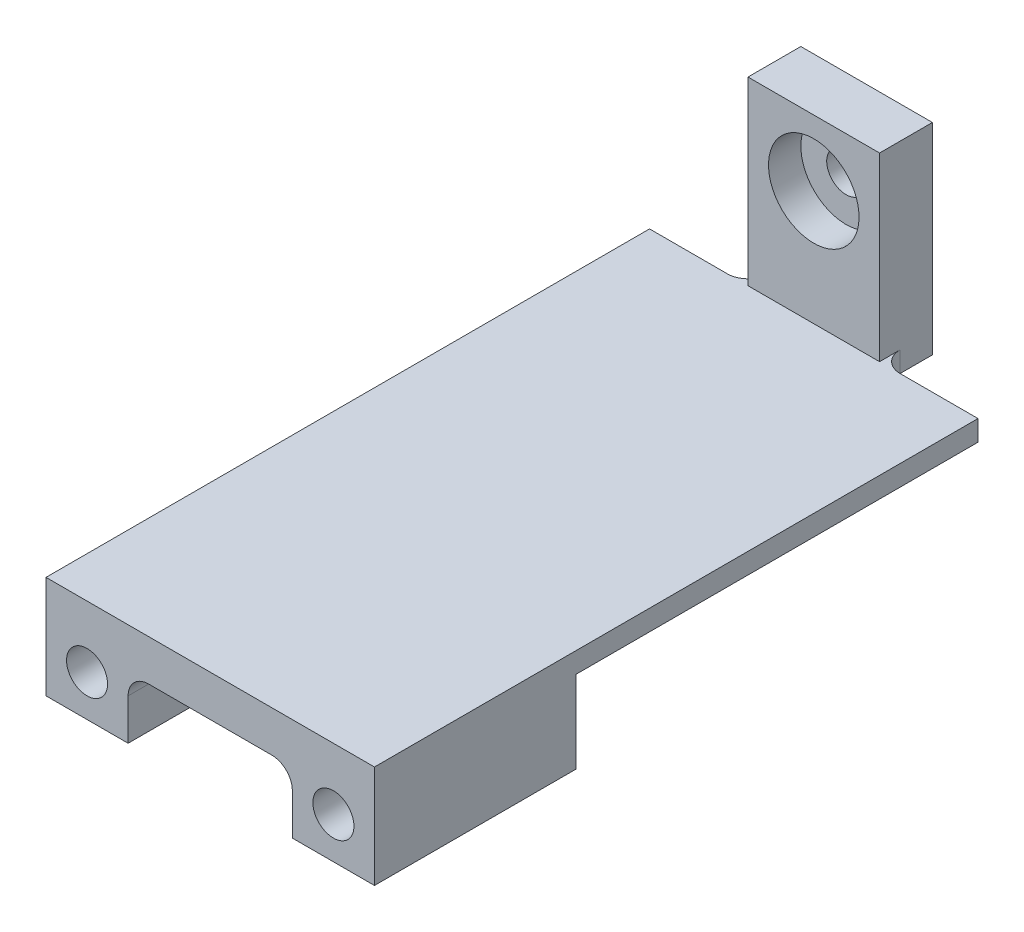
SolidWorks part; units mm, degrees
material "6061-T6 (SS)"
ref_plane "Front Plane" through (0, 0, 0) normal (0, 0, 1) x (1, 0, 0)
ref_plane "Top Plane" through (0, 0, 0) normal (0, 1, 0) x (1, 0, 0)
ref_plane "Right Plane" through (0, 0, 0) normal (1, 0, 0) x (0, 0, -1)
sketch "Sketch1" plane through (0, 0, 0) normal (0, 1, 0) x (1, 0, 0)
  line L1 (-88.9, -50.8) -> (88.9, -50.8)
  line L2 (-88.9, -50.8) -> (-88.9, 50.8)
  line L3 (-88.9, 50.8) -> (88.9, 50.8)
  line L4 (88.9, -50.8) -> (88.9, 50.8)
  line L5 (-88.9, -50.8) -> (88.9, 50.8) construction
  line L6 (-88.9, 50.8) -> (88.9, -50.8) construction
  point P0 (0, 0)
  dimension "D1" = 101.6
  dimension "D2" = 177.8
extrude "Boss-Extrude1" add sketch "Sketch1" along normal blind 12.7
sketch "Sketch2" plane through (0, 0, 50.8) normal (0, 0, 1) x (1, 0, 0)
  line L0 (12.7, -19.05) -> (12.7, 0)
  line L1 (-88.9, 0) -> (88.9, 0) construction
  line L3 (12.7, -19.05) -> (-12.7, -19.05)
  line L4 (-12.7, -19.05) -> (-12.7, 0)
  line L5 (12.7, 0) -> (-12.7, 0)
  point P0 (0, 0)
  point P2 (0, -19.05)
  dimension "D2" = 25.4
  dimension "D3" = 19.05
extrude "Boss-Extrude2" add sketch "Sketch2" against normal up to surface (101.6 mm away) up to face at (0, 6.35, -50.8)
sketch "Sketch3" plane through (0, 0, 50.8) normal (0, 0, 1) x (1, 0, 0)
  line L0 (0, 0) -> (0, -6.35) construction
  circle A1 centre (0, -6.35) radius 6.35
  point P4 (0, -3.175)
  dimension "D2" = 12.7
  dimension "D1" = 6.35
extrude "Cut-Extrude1" cut sketch "Sketch3" against normal up to surface (101.6 mm away) up to face at (0, -1.5875, -50.8)
sketch "Sketch4" plane through (0, 0, 50.8) normal (0, 0, 1) x (1, 0, 0)
  line L0 (-88.9, 0) -> (-12.7, 0) construction
  line L3 (-88.9, 0) -> (-88.9, -19.05)
  line L4 (-88.9, -19.05) -> (-63.5, -19.05)
  line L5 (-63.5, -19.05) -> (-63.5, 0)
  line L6 (-63.5, 0) -> (-88.9, 0)
  point P0 (-76.2, 0)
  point P4 (0, 0)
  dimension "D3" = 19.05
  dimension "D2" = 76.2
  dimension "D4" = 25.4
extrude "Boss-Extrude3" add sketch "Sketch4" against normal up to surface (101.6 mm away) up to face at (6.35, -6.35, -50.8)
mirror "Mirror1" about plane through (0, 0, 0) normal (1, 0, 0) of "Boss-Extrude3"
sketch "Sketch5" plane through (0, 0, 50.8) normal (0, 0, 1) x (1, 0, 0)
  circle A0 centre (-76.2, -6.35) radius 6.35
  circle A1 centre (76.2, -6.35) radius 6.35
  point P0 (-76.2, -6.35)
  point P1 (76.2, -6.35)
  dimension "D4" = 12.7
  dimension "D1" = 76.2
  dimension "D2" = 76.2
  dimension "D3" = 6.35
extrude "Cut-Extrude2" cut sketch "Sketch5" against normal up to surface (101.6 mm away) up to face at (6.35, -6.35, -50.8)
sketch "Sketch6" plane through (0, 0, -50.8) normal (0, 0, -1) x (-1, 0, 0)
  line L1 (12.7, -19.05) -> (88.9, -19.05)
  line L2 (12.7, -19.05) -> (12.7, 12.7)
  line L3 (12.7, 12.7) -> (88.9, 12.7)
  line L4 (88.9, -19.05) -> (88.9, 12.7)
extrude "Cut-Extrude3" cut sketch "Sketch6" against normal up to surface (101.6 mm away) up to face at (-69.85, -6.35, 50.8)
fillet "Fillet1" radius 6.35 2 edges at (63.5, 0, 0) (12.7, 0, 0)
sketch "Sketch8" plane through (0, 0, -50.8) normal (0, 0, -1) x (-1, 0, 0)
  line L0 (12.7, -19.05) -> (12.7, 12.7) construction
  line L1 (-88.9, 12.7) -> (12.7, 12.7)
  line L2 (-88.9, 12.7) -> (-88.9, 0)
  line L3 (-88.9, 0) -> (12.7, 0)
  line L4 (12.7, 12.7) -> (12.7, 0)
extrude "Boss-Extrude5" add sketch "Sketch8" along normal blind 85.09
sketch "Sketch9" plane through (0, 0, -135.89) normal (0, 0, -1) x (-1, 0, 0)
  line L0 (12.7, 12.7) -> (-88.9, 12.7) construction
  line L1 (-88.9, 0) -> (12.7, 0) construction
  line L2 (-17.75, 0) -> (-58.45, 0)
  line L3 (-17.75, 0) -> (-17.75, 68.61)
  line L4 (-17.75, 68.61) -> (-58.45, 68.61)
  line L5 (-58.45, 0) -> (-58.45, 68.61)
  line L6 (12.7, 0) -> (12.7, 12.7) construction
  circle A0 centre (-38.1, 48.26) radius 6
  circle A1 centre (-38.1, 48.26) radius 14 construction
  point P0 (-38.1, 12.7)
  point P9 (-38.1, 48.26)
  point P10 (-38.1, 0)
  point P14 (-38.1, 62.26)
  dimension "D3" = 12
  dimension "D4" = 6.35
  dimension "D5" = 28
  dimension "D1" = 40.7
  dimension "D2" = 35.56
  dimension "D6" = 50.8
extrude "Boss-Extrude6" add sketch "Sketch9" along normal blind 16.35
sketch "Sketch10" plane through (0, 0, -135.89) normal (0, 0, 1) x (1, 0, 0)
  circle A0 centre (38.1, 48.26) radius 14
  dimension "D1" = 28
extrude "Cut-Extrude4" cut sketch "Sketch10" against normal blind 10
fillet "Fillet2" radius 6.35 2 edges at (58.45, 6.35, -135.89) (17.75, 6.35, -135.89)
sketch "Sketch11" plane through (0, 0, 0) normal (0, -1, 0) x (1, 0, 0)
  line L1 (88.9, -50.8) -> (-17.0265, -50.8)
  line L2 (88.9, -50.8) -> (88.9, -160.0192)
  line L3 (88.9, -160.0192) -> (-17.0265, -160.0192)
  line L4 (-17.0265, -50.8) -> (-17.0265, -160.0192)
extrude "Cut-Extrude5" cut sketch "Sketch11" against normal blind 6.35
fillet "Fillet3" radius 3.175 1 edges at (38.1, 6.35, -50.8)
sketch "Sketch12" plane through (0, 0, -50.8) normal (0, 0, -1) x (-1, 0, 0)
  line L0 (12.7, -19.05) -> (12.7, 3.175) construction
  line L1 (-88.9, -19.05) -> (12.7, -19.05)
  line L2 (-88.9, -19.05) -> (-88.9, 6.35)
  line L3 (-88.9, 6.35) -> (12.7, 6.35)
  line L4 (12.7, -19.05) -> (12.7, 6.35)
  dimension "D1" = 25.4
extrude "Cut-Extrude6" cut sketch "Sketch12" against normal blind 39.25 and the other way blind 3.175
